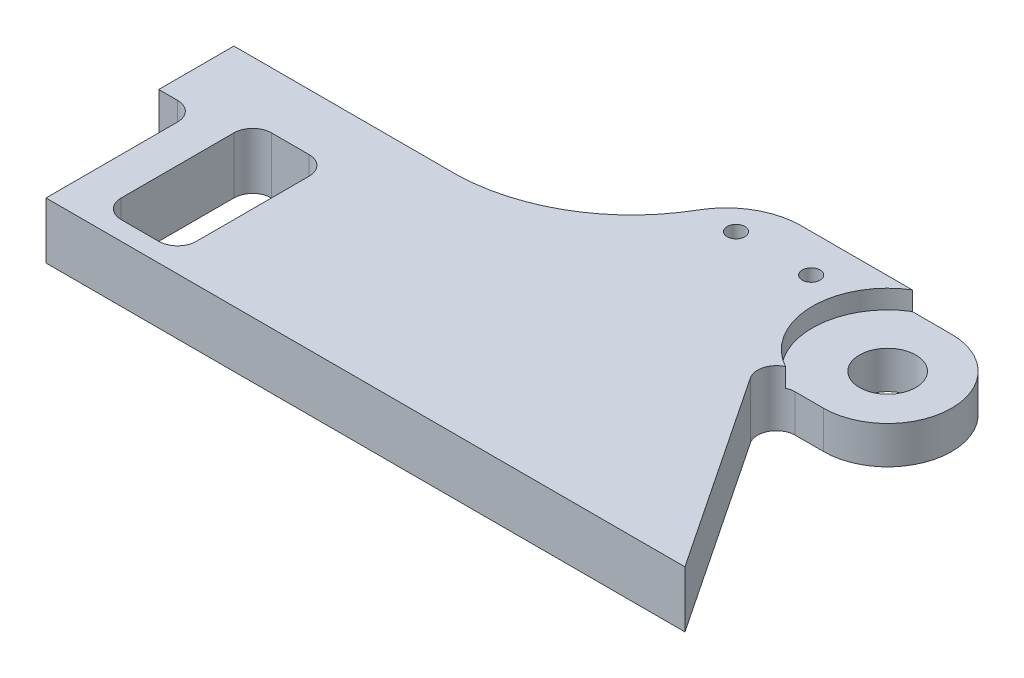
SolidWorks part; units mm, degrees
material "UHMW"
ref_plane "Front Plane" through (0, 0, 0) normal (0, 0, 1) x (1, 0, 0)
ref_plane "Top Plane" through (0, 0, 0) normal (0, 1, 0) x (1, 0, 0)
ref_plane "Right Plane" through (0, 0, 0) normal (1, 0, 0) x (0, 0, -1)
other "Bounding Box"
ref_plane "Default Plane" through (-8.9266, -12.7485, 0) normal (-0.1736, 0.9848, 0) x (0.9848, 0.1736, 0)
sketch "Sketch1" plane through (0, 0, 0) normal (0, 1, 0) x (1, 0, 0)
  line L0 (0, 0) -> (38.1, 0)
  line L1 (88.9, 0) -> (114.3, -38.1)
  line L2 (114.3, -38.1) -> (6.35, -38.1)
  line L3 (6.35, -38.1) -> (6.35, -12.7)
  line L4 (6.35, -12.7) -> (0, -12.7)
  line L5 (0, -12.7) -> (0, 0)
  line L6 (99.6289, 0) -> (88.9, 0)
  line L9 (99.6289, 21.632) -> (74.2289, 21.632)
  circle A0 centre (99.6289, 10.816) radius 4.7625
  arc A1 (99.6289, 21.632) -> (99.6289, 0) centre (99.6289, 10.816) cw
  arc A4 (74.2289, 21.632) -> (63.2185, 15.2614) centre (74.2289, 8.932) ccw
  arc A5 (63.2185, 15.2614) -> (38.1, 0) centre (36.7936, 30.452) cw
  circle A6 centre (69.5685, 15.2614) radius 1.5
  circle A7 centre (82.2685, 15.2614) radius 1.5
  dimension "D7" = 50.8
  dimension "D8" = 9.525
  dimension "D9" = 10.7289
  dimension "D6" = 10.816
  dimension "D10" = 30.48
  dimension "D16" = 12.7
  dimension "D19" = 3
  dimension "D1" = 6.35
  dimension "D2" = 38.1
  dimension "D3" = 107.95
  dimension "D4" = 88.9
  dimension "D5" = 12.7
  dimension "D17" = 38.1
  dimension "D18" = 25.4
  dimension "D20" = 6.35
  dimension "D21" = 12.7
extrude "Boss-Extrude1" add sketch "Sketch1" along normal blind 9.525
fillet "Fillet1" radius 3.175 1 edges at (88.9, 4.7625, 0)
fillet "Fillet2" radius 3.175 1 edges at (6.35, 4.7625, 12.7)
sketch "Sketch3" plane through (0, 9.525, 0) normal (0, 1, 0) x (1, 0, 0)
  circle A4 centre (99.6289, 10.816) radius 12.7
  dimension "D1" = 25.4
extrude "Cut-Extrude2" cut sketch "Sketch3" against normal blind 3.175
sketch "Sketch4" plane through (0, 9.525, 0) normal (0, 1, 0) x (1, 0, 0)
  line L0 (12.7, -9.525) -> (12.7, -34.925)
  line L1 (12.7, -34.925) -> (25.4, -34.925)
  line L2 (25.4, -34.925) -> (25.4, -9.525)
  line L3 (25.4, -9.525) -> (12.7, -9.525)
  line L4 (6.35, -38.1) -> (114.3, -38.1) construction
  line L5 (6.35, -15.875) -> (6.35, -38.1) construction
  dimension "D1" = 25.4
  dimension "D2" = 12.7
  dimension "D3" = 3.175
  dimension "D4" = 6.35
extrude "Cut-Extrude3" cut sketch "Sketch4" against normal through all
fillet "Fillet3" radius 3.175 4 edges at (25.4, 4.7625, 34.925) (12.7, 4.7625, 34.925) (12.7, 4.7625, 9.525) (25.4, 4.7625, 9.525)
